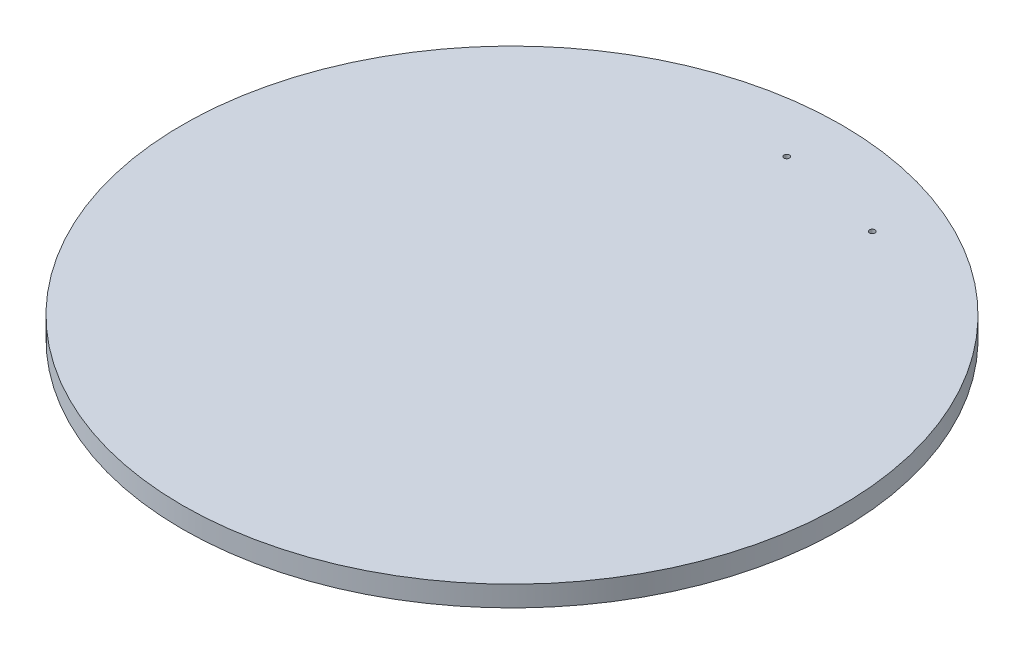
SolidWorks part; units mm, degrees
ref_plane "Front Plane" through (0, 0, 0) normal (0, 0, 1) x (1, 0, 0)
ref_plane "Top Plane" through (0, 0, 0) normal (0, 1, 0) x (1, 0, 0)
ref_plane "Right Plane" through (0, 0, 0) normal (1, 0, 0) x (0, 0, -1)
sketch "Sketch2" plane through (0, 0, 0) normal (0, 1, 0) x (1, 0, 0)
  circle A0 centre (0, 0) radius 304.8
extrude "Boss-Extrude1" add sketch "Sketch2" along normal blind 19.05
sketch "Sketch3" plane through (0, 19.05, 0) normal (0, 1, 0) x (1, 0, 0)
  circle A0 centre (0, 254) radius 2.54
  circle A1 centre (99.5473, 233.68) radius 2.54
  dimension "D1" = 254
  dimension "D2" = 254
  dimension "D3" = 101.6
extrude "Cut-Extrude1" cut sketch "Sketch3" against normal through all
